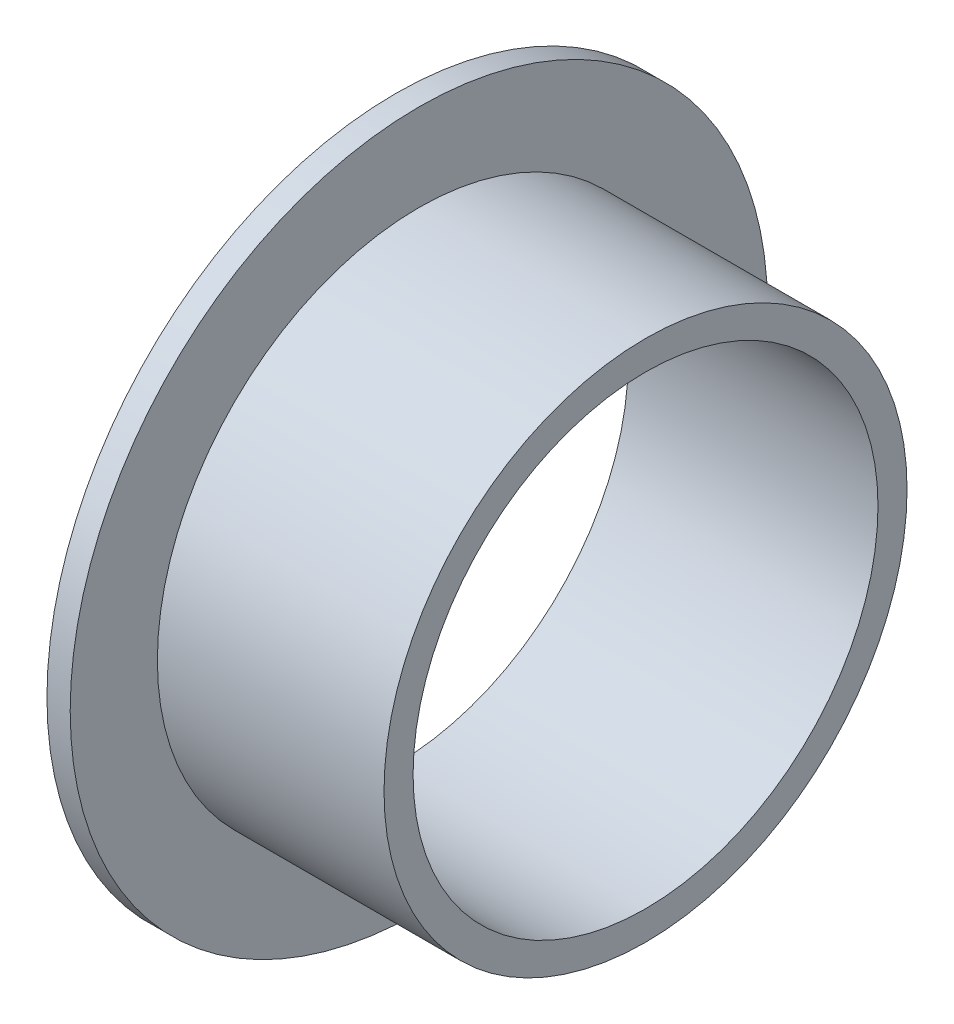
SolidWorks part; units mm, degrees
material "Bronze Cu Sn 8 P"
ref_plane "Face" through (0, 0, 0) normal (0, 0, 1) x (1, 0, 0)
ref_plane "Dessus" through (0, 0, 0) normal (0, 1, 0) x (1, 0, 0)
ref_plane "Droite" through (0, 0, 0) normal (1, 0, 0) x (0, 0, -1)
sketch "Esquisse1" plane through (0, 0, 0) normal (0, 0, 1) x (1, 0, 0)
  line L0 (0, 8) -> (8.6, 8)
  line L1 (8.6, 8) -> (8.6, 9)
  line L2 (8.6, 9) -> (0.8, 9)
  line L3 (0.8, 9) -> (0.8, 12)
  line L4 (0.8, 12) -> (0, 12)
  line L5 (0, 12) -> (0, 8)
  line L6 (0, 0) -> (15.3907, 0) construction
  dimension "D1" = 16
  dimension "D2" = 18
  dimension "D3" = 24
  dimension "D4" = 7.8
  dimension "D5" = 0.8
revolve "Révolution1" add sketch "Esquisse1" angle 360 about L6
